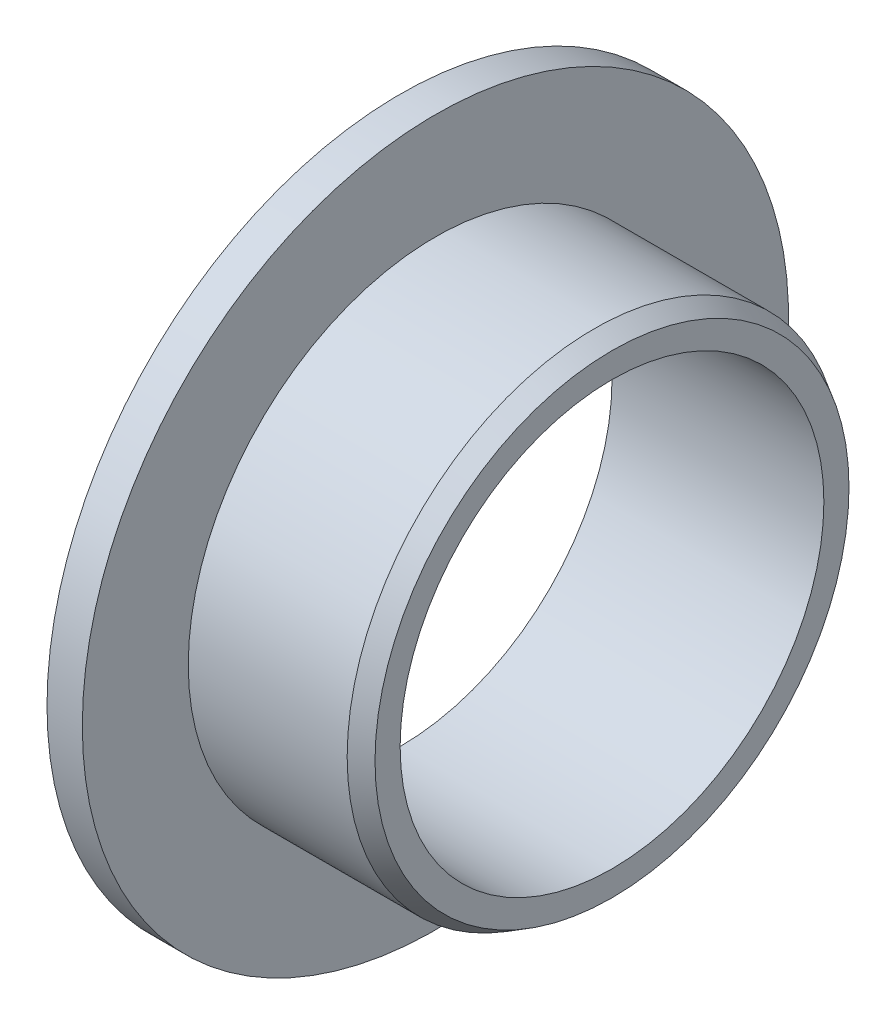
SolidWorks part; units mm, degrees
ref_plane "Płaszczyzna przednia" through (0, 0, 0) normal (0, 0, 1) x (1, 0, 0)
ref_plane "Płaszczyzna górna" through (0, 0, 0) normal (0, 1, 0) x (1, 0, 0)
ref_plane "Płaszczyzna prawa" through (0, 0, 0) normal (1, 0, 0) x (0, 0, -1)
sketch "Szkic1" plane through (0, 0, 0) normal (0, 0, 1) x (1, 0, 0)
  line L0 (0, 0) -> (0, 6) construction
  line L1 (0, 6) -> (6, 6)
  line L2 (0, 0) -> (24.2255, 0) construction
  line L3 (6, 6) -> (6, 7)
  line L4 (6, 7) -> (1, 7)
  line L5 (0, 6) -> (0, 10)
  line L6 (0, 10) -> (1, 10)
  line L7 (1, 10) -> (1, 7)
  point P10 (1, 8.5)
  dimension "D1" = 6
  dimension "D2" = 7
  dimension "D3" = 10
  dimension "D4" = 1
  dimension "D5" = 6
revolve "Obrót1" add sketch "Szkic1" angle 360 about L2
chamfer "Sfazowanie1" distance 0.5 angle 30 1 edges at (6, 0, 7)
